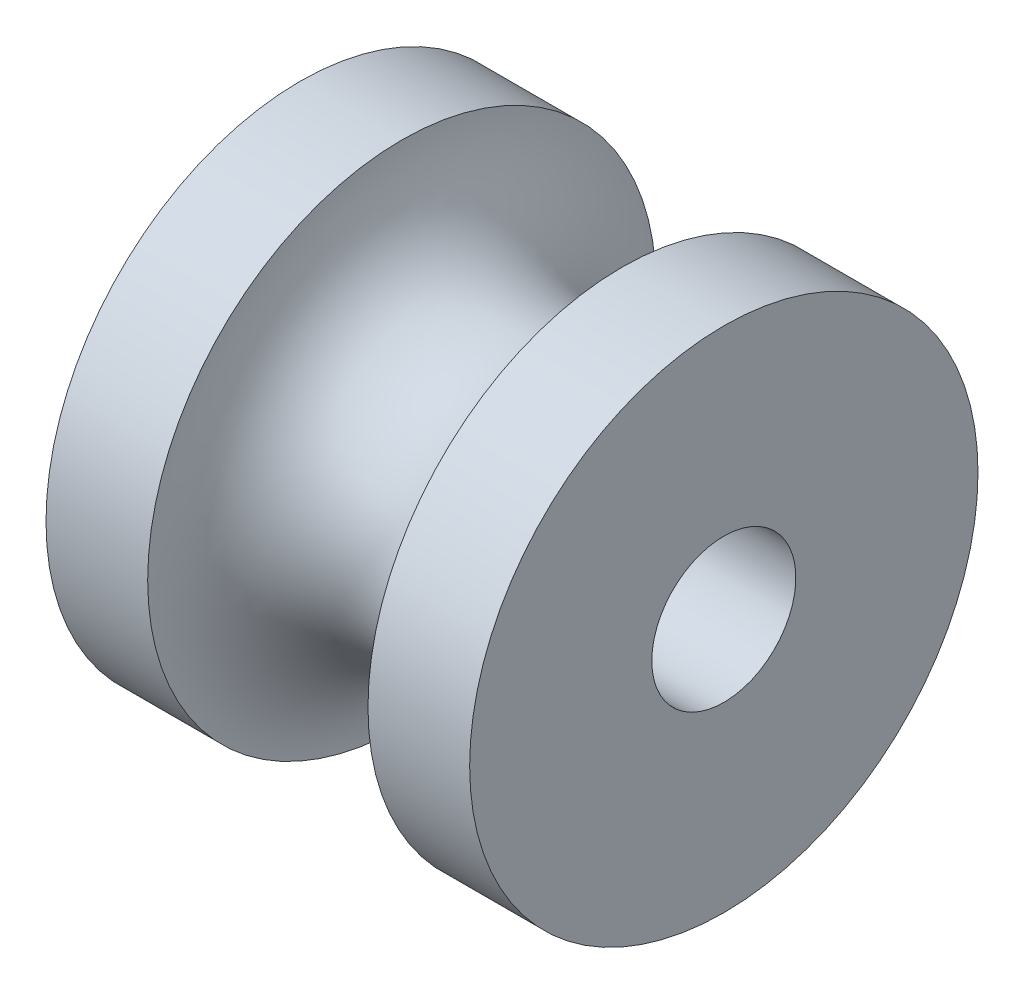
SolidWorks part; units mm, degrees
ref_plane "Plan de face" through (0, 0, 0) normal (0, 0, 1) x (1, 0, 0)
ref_plane "Plan de dessus" through (0, 0, 0) normal (0, 1, 0) x (1, 0, 0)
ref_plane "Plan de droite" through (0, 0, 0) normal (1, 0, 0) x (0, 0, -1)
sketch "Esquisse2" plane through (0, 0, 0) normal (0, 0, 1) x (1, 0, 0)
  line L0 (-5, -6) -> (-2.6, -6)
  line L1 (-5, -1.7) -> (5, -1.7)
  line L2 (-5, -1.7) -> (-5, -6)
  line L3 (-5, -6) -> (5, -6) construction
  line L4 (5, -1.7) -> (5, -6)
  line L5 (5, -6) -> (2.6, -6)
  line L6 (-9.5995, 0) -> (21.5663, 0) construction
  line L7 (0, -6) -> (0, 0) construction
  arc A0 (-2.6, -6) -> (2.6, -6) centre (0, -6) cw
  dimension "D1" = 6
  dimension "D2" = 2.6
  dimension "D3" = 10
  dimension "D4" = 1.7
revolve "Révolution1" add sketch "Esquisse2" angle 360 about L6
